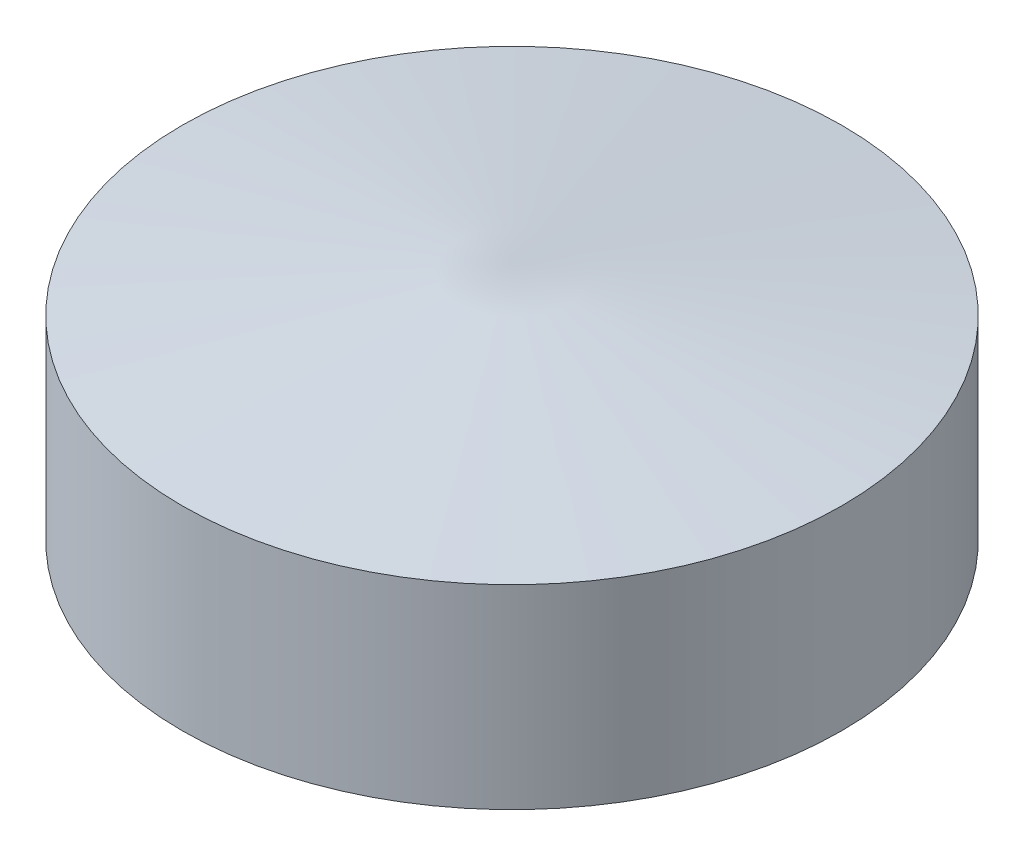
SolidWorks part; units mm, degrees
ref_plane "Front Plane" through (0, 0, 0) normal (0, 0, 1) x (1, 0, 0)
ref_plane "Top Plane" through (0, 0, 0) normal (0, 1, 0) x (1, 0, 0)
ref_plane "Right Plane" through (0, 0, 0) normal (1, 0, 0) x (0, 0, -1)
sketch "Sketch2" plane through (0, 0, 0) normal (0, 0, 1) x (1, 0, 0)
  line L0 (0, 0) -> (0, 128.2) construction
  line L1 (0, 0) -> (22, 0)
  line L2 (22, 0) -> (22, 13)
  line L3 (22, 13) -> (0, 16)
  line L4 (0, 16) -> (0, 0)
  dimension "D1" = 13
  dimension "D2" = 44
  dimension "D3" = 3
revolve "Revolve1" add sketch "Sketch2" angle 360 about L0
sketch "Sketch3" plane through (0, 0, 0) normal (0, 1, 0) x (1, 0, 0)
  circle A0 centre (-22, 0) radius 1.5
  dimension "D1" = 3
  dimension "D2" = 22
extrude "Cut-Extrude1" cut sketch "Sketch3" along normal blind 10
